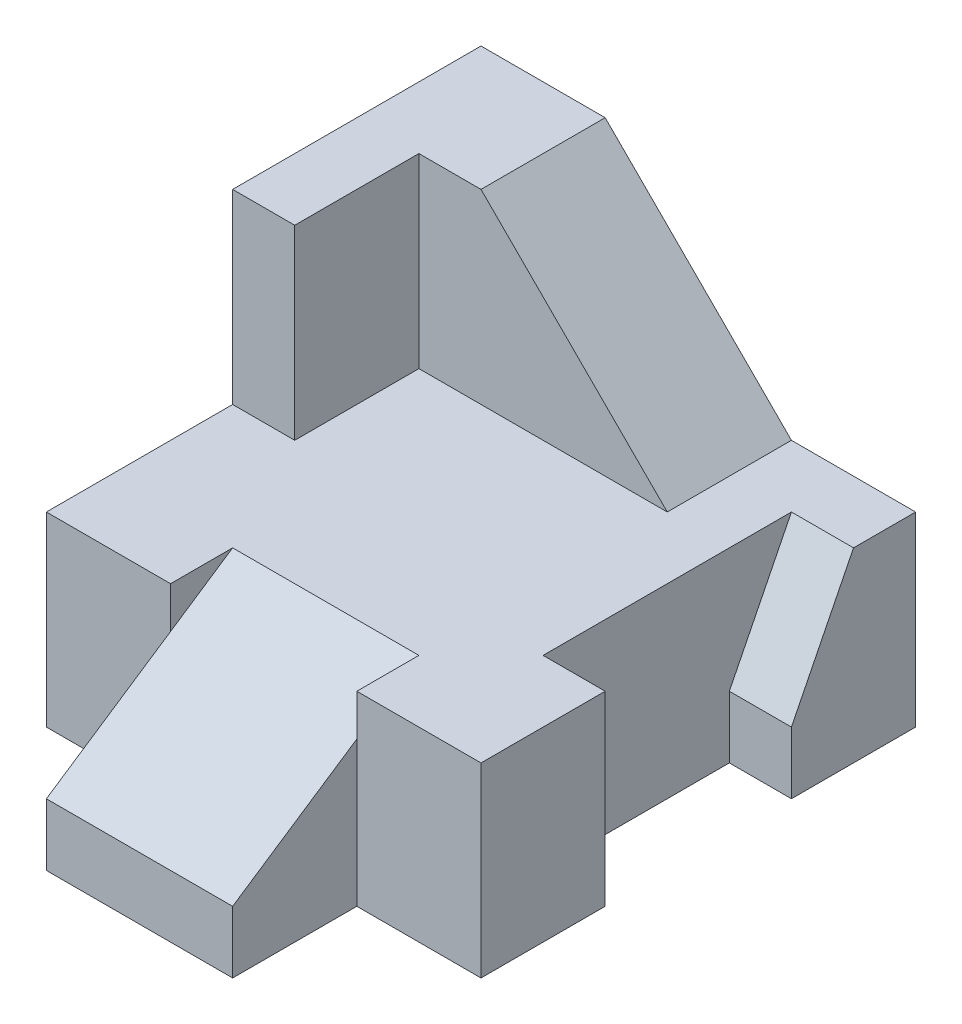
SolidWorks part; units mm, degrees
ref_plane "Front Plane" through (0, 0, 0) normal (0, 0, 1) x (1, 0, 0)
ref_plane "Top Plane" through (0, 0, 0) normal (0, 1, 0) x (1, 0, 0)
ref_plane "Right Plane" through (0, 0, 0) normal (1, 0, 0) x (0, 0, -1)
sketch "Sketch1" plane through (0, 0, 0) normal (0, 0, 1) x (1, 0, 0)
  line L1 (3.5, -3) -> (-3.5, -3)
  line L2 (3.5, -3) -> (3.5, 3)
  line L3 (3.5, 3) -> (-3.5, 3)
  line L4 (-3.5, -3) -> (-3.5, 3)
  line L5 (3.5, -3) -> (-3.5, 3) construction
  line L6 (3.5, 3) -> (-3.5, -3) construction
  point P0 (0, 0)
  dimension "D1" = 7
  dimension "D2" = 6
extrude "Boss-Extrude1" add sketch "Sketch1" along normal blind 9
sketch "Sketch2" plane through (0, 3, 0) normal (0, 1, 0) x (1, 0, 0)
  line L0 (-3.5, -9) -> (-3.5, -7)
  line L1 (-3.5, -9) -> (-3.5, 0) construction
  line L2 (-3.5, -7) -> (-1.5, -7)
  line L3 (-1.5, -7) -> (-1.5, -9)
  line L4 (3.5, -9) -> (-3.5, -9) construction
  line L5 (-1.5, -9) -> (-3.5, -9)
  line L6 (3.5, -9) -> (3.5, -7)
  line L7 (3.5, -9) -> (3.5, 0) construction
  line L8 (3.5, -7) -> (1.5, -7)
  line L9 (1.5, -7) -> (1.5, -9)
  line L10 (1.5, -9) -> (3.5, -9)
  line L11 (3.5, -2) -> (2.5, -2)
  line L12 (2.5, -2) -> (2.5, -5)
  line L13 (2.5, -5) -> (3.5, -5)
  line L14 (3.5, -5) -> (3.5, -2)
  dimension "D1" = 2
  dimension "D2" = 2
  dimension "D3" = 2
  dimension "D4" = 1
  dimension "D5" = 2
  dimension "D6" = 3
extrude "Cut-Extrude1" cut sketch "Sketch2" against normal through all
sketch "Sketch3" plane through (0, 3, 0) normal (0, 1, 0) x (1, 0, 0)
  line L0 (1.5, 0) -> (1.5, -2)
  line L1 (3.5, 0) -> (-3.5, 0) construction
  line L2 (1.5, -2) -> (-2.5, -2)
  line L3 (-2.5, -2) -> (-2.5, -4)
  line L4 (-2.5, -4) -> (-3.5, -4)
  line L5 (-3.5, -7) -> (-3.5, 0) construction
  line L6 (-3.5, -4) -> (-3.5, 0)
  line L7 (-3.5, 0) -> (1.5, 0)
  dimension "D1" = 2
  dimension "D2" = 2
  dimension "D3" = 1
  dimension "D4" = 2
extrude "Cut-Extrude3" cut sketch "Sketch3" against normal blind 3 flip side to cut
sketch "Sketch4" plane through (0, 0, 2) normal (0, 0, 1) x (1, 0, 0)
  line L0 (-1.5, 3) -> (1.5, 0)
  line L1 (-2.5, 3) -> (1.5, 3) construction
  line L2 (1.5, 0) -> (1.5, 3)
  line L3 (1.5, 3) -> (-1.5, 3)
  dimension "D1" = 1
extrude "Cut-Extrude4" cut sketch "Sketch4" against normal blind 3
sketch "Sketch5" plane through (3.5, 0, 0) normal (1, 0, 0) x (0, 0, -1)
  line L0 (-1, 0) -> (-2, -2)
  line L1 (-2, 0) -> (0, 0) construction
  line L2 (-2, -3) -> (-2, 0) construction
  line L3 (-2, -2) -> (-2, 0)
  line L4 (-2, 0) -> (-1, 0)
  dimension "D1" = 1
extrude "Cut-Extrude5" cut sketch "Sketch5" against normal blind 1
sketch "Sketch6" plane through (0, 0, 0) normal (0, 1, 0) x (1, 0, 0)
  line L0 (1.5, -6) -> (-1.5, -6)
  line L1 (-3.5, -7) -> (-1.5, -7) construction
  dimension "D1" = 1
sketch "Sketch7" plane through (0, 0, 9) normal (0, 0, 1) x (1, 0, 0)
  line L0 (1.5, -2) -> (-1.5, -2)
  line L1 (1.5, -3) -> (1.5, 0) construction
  line L2 (-1.5, -3) -> (-1.5, 0) construction
  dimension "D1" = 1
ref_plane "Plane1" through (0, 2.7692, 1.8462) normal (0, 0.8321, 0.5547) x (1, 0, 0)
sketch "Sketch8" plane through (0, 2.7692, 1.8462) normal (0, 0.8321, 0.5547) x (1, 0, 0)
  line L0 (1.5, -4.9923) -> (-1.5, -4.9923)
  line L1 (-1.5, -4.9923) -> (-1.5, -8.5979)
  line L2 (-1.5, -8.5979) -> (1.5, -8.5979)
  line L3 (1.5, -8.5979) -> (1.5, -4.9923)
extrude "Cut-Extrude6" cut sketch "Sketch8" along normal through all
